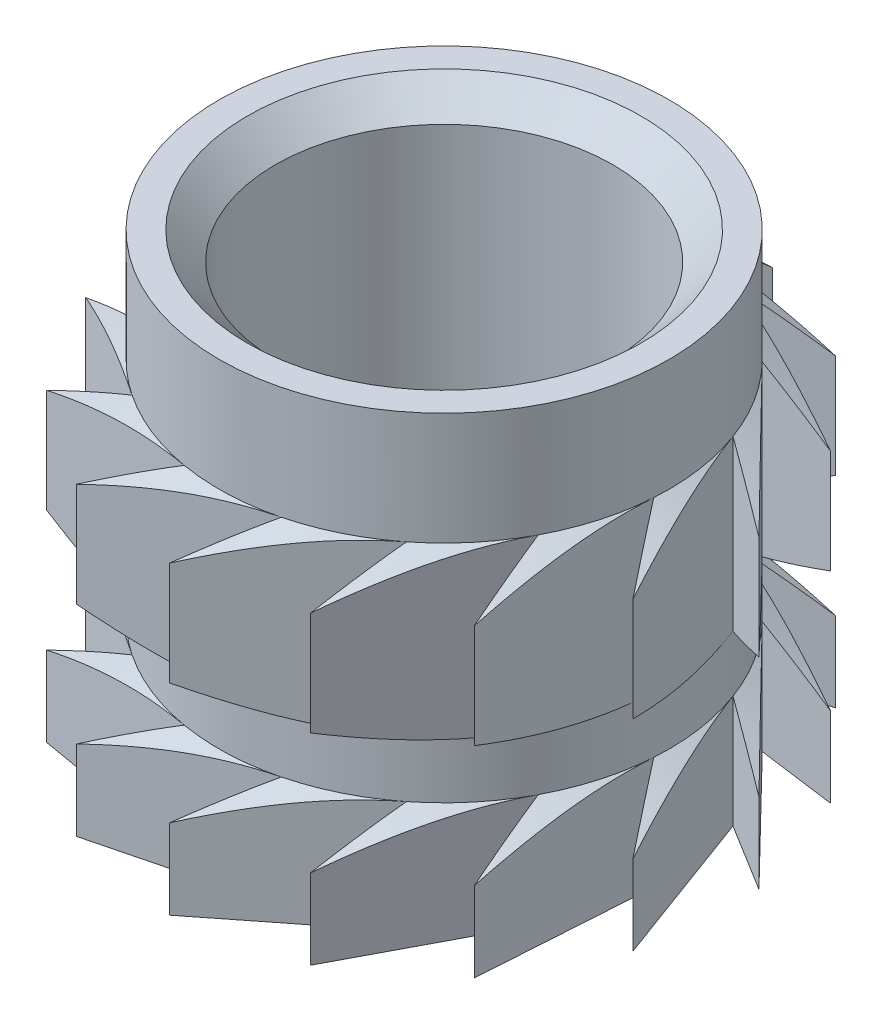
SolidWorks part; units mm, degrees
ref_plane "Front Plane" through (0, 0, 0) normal (0, 0, 1) x (1, 0, 0)
ref_plane "Top Plane" through (0, 0, 0) normal (0, 1, 0) x (1, 0, 0)
ref_plane "Right Plane" through (0, 0, 0) normal (1, 0, 0) x (0, 0, -1)
sketch "Sketch1" plane through (0, 0, 0) normal (0, 1, 0) x (1, 0, 0)
  circle A0 centre (0, 0) radius 1.5
  circle A1 centre (0, 0) radius 2
  dimension "D1" = 3
  dimension "D2" = 4
extrude "Boss-Extrude1" add sketch "Sketch1" along normal blind 4
sketch "Sketch2" plane through (0, 0, 0) normal (0, 0, 1) x (1, 0, 0)
  line L0 (-2, 0) -> (2, 0) construction
  line L1 (-2, 4) -> (-2, 0) construction
  line L2 (2, 4) -> (-2, 4) construction
  line L3 (2, 0) -> (2, 4) construction
  line L4 (-2, 0) -> (2, 0) construction
  line L5 (-2, 4) -> (-2, 0) construction
  line L6 (2, 4) -> (-2, 4) construction
  line L7 (2, 0) -> (2, 4) construction
  line L8 (2, 3) -> (2.5, 2.7113)
  line L9 (2.5, 2.7113) -> (2.5, 1.7887)
  line L10 (2.5, 1.7887) -> (2, 1.5)
  line L11 (2, 0) -> (2.5, 0)
  line L12 (2.5, 0) -> (2.5, 0.7113)
  line L13 (2.5, 0.7113) -> (2, 1)
  line L14 (2, 1) -> (2, 0)
  line L15 (2, 1.5) -> (2, 3)
  line L16 (0, 0) -> (0, 50000) construction
  dimension "D1" = 1
  dimension "D2" = 1.5
  dimension "D3" = 1
  dimension "D4" = 0.5
  dimension "D5" = 60
  dimension "D6" = 60
  dimension "D7" = 60
revolve "Revolve1" add sketch "Sketch2" angle 360 about L16
sketch "Sketch3" plane through (0, 4, 0) normal (0, 1, 0) x (1, 0, 0)
  line L0 (-0.0773, 1.9985) -> (1.4216, 2.0565)
  line L1 (1.4216, 2.0565) -> (0.7422, 1.8572)
  line L2 (0.7422, 1.8572) -> (2.1351, 1.3005)
  line L3 (2.1351, 1.3005) -> (1.4335, 1.3947)
  line L4 (1.4335, 1.3947) -> (2.4795, 0.3196)
  line L5 (2.4795, 0.3196) -> (1.8768, 0.6911)
  line L6 (1.8768, 0.6911) -> (2.3951, -0.7165)
  line L7 (2.3951, -0.7165) -> (1.9956, -0.132)
  line L8 (1.9956, -0.132) -> (1.8966, -1.6288)
  line L9 (1.8966, -1.6288) -> (1.7694, -0.9323)
  line L10 (1.7694, -0.9323) -> (1.0702, -2.2594)
  line L11 (1.0702, -2.2594) -> (1.2372, -1.5714)
  line L12 (1.2372, -1.5714) -> (0.0587, -2.4993)
  line L13 (0.0587, -2.4993) -> (0.4911, -1.9388)
  line L14 (0.4911, -1.9388) -> (-0.9629, -2.3071)
  line L15 (-0.9629, -2.3071) -> (-0.3399, -1.9709)
  line L16 (-0.3399, -1.9709) -> (-1.8181, -1.716)
  line L17 (-1.8181, -1.716) -> (-1.1122, -1.6623)
  line L18 (-1.1122, -1.6623) -> (-2.3589, -0.8281)
  line L19 (-2.3589, -0.8281) -> (-1.6921, -1.0662)
  line L20 (-1.6921, -1.0662) -> (-2.4918, 0.2029)
  line L21 (-2.4918, 0.2029) -> (-1.9795, -0.2858)
  line L22 (-1.9795, -0.2858) -> (-2.1938, 1.1988)
  line L23 (-2.1938, 1.1988) -> (-1.9246, 0.5441)
  line L24 (-1.9246, 0.5441) -> (-1.5165, 1.9875)
  line L25 (-1.5165, 1.9875) -> (-1.5369, 1.2798)
  line L26 (-1.5369, 1.2798) -> (-0.577, 2.4325)
  line L27 (-0.577, 2.4325) -> (-0.8835, 1.7943)
  line L28 (-0.8835, 1.7943) -> (0.4622, 2.4569)
  line L29 (0.4622, 2.4569) -> (-0.0773, 1.9985)
  circle A0 centre (0, 0) radius 2 construction
  circle A1 centre (0, 0) radius 2 construction
  circle A2 centre (0, 0) radius 2.5 construction
  arc A3 (-0.0773, 1.9985) -> (0.7422, 1.8572) centre (0, 0) cw
  arc A4 (0.7422, 1.8572) -> (1.4335, 1.3947) centre (0, 0) cw
  arc A5 (1.4335, 1.3947) -> (1.8768, 0.6911) centre (0, 0) cw
  arc A6 (1.8768, 0.6911) -> (1.9956, -0.132) centre (0, 0) cw
  arc A7 (1.9956, -0.132) -> (1.7694, -0.9323) centre (0, 0) cw
  arc A8 (1.7694, -0.9323) -> (1.2372, -1.5714) centre (0, 0) cw
  arc A9 (1.2372, -1.5714) -> (0.4911, -1.9388) centre (0, 0) cw
  arc A10 (0.4911, -1.9388) -> (-0.3399, -1.9709) centre (0, 0) cw
  arc A11 (-0.3399, -1.9709) -> (-1.1122, -1.6623) centre (0, 0) cw
  arc A12 (-1.1122, -1.6623) -> (-1.6921, -1.0662) centre (0, 0) cw
  arc A13 (-1.6921, -1.0662) -> (-1.9795, -0.2858) centre (0, 0) cw
  arc A14 (-1.9795, -0.2858) -> (-1.9246, 0.5441) centre (0, 0) cw
  arc A15 (-1.9246, 0.5441) -> (-1.5369, 1.2798) centre (0, 0) cw
  arc A16 (-1.5369, 1.2798) -> (-0.8835, 1.7943) centre (0, 0) cw
  arc A17 (-0.8835, 1.7943) -> (-0.0773, 1.9985) centre (0, 0) cw
  circle A18 centre (0, 0) radius 2.5
  circle A19 centre (0, 0) radius 2 construction
  point P53 (0, 0)
  dimension "D1" = 15
extrude "Cut-Extrude3" cut sketch "Sketch3" against normal through all contours L28 A18 L27 | L0 A18 L29 | L2 A18 L1 | L4 A18 L3 | L6 A18 L5 | L8 A18 L7 | L10 A18 L9 | L12 A18 L11 | L14 A18 L13 | L16 A18 L15 | L18 A18 L17 | L20 A18 L19 | L22 A18 L21 | L24 A18 L23 | L26 A18 L25
chamfer "Chamfer1" distance 0.25 angle 45 2 edges at (0, 4, 1.5) (0, 0, 1.5)
